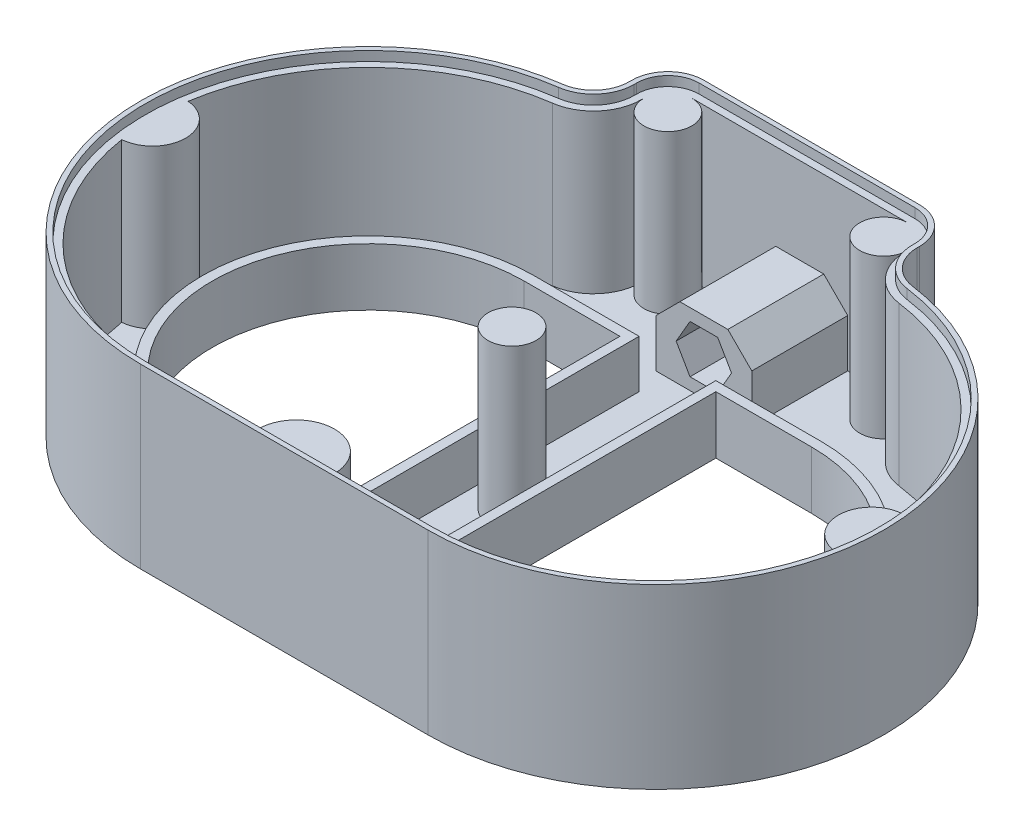
SolidWorks part; units mm, degrees
ref_plane "Front Plane" through (0, 0, 0) normal (0, 0, 1) x (1, 0, 0)
ref_plane "Top Plane" through (0, 0, 0) normal (0, 1, 0) x (1, 0, 0)
ref_plane "Right Plane" through (0, 0, 0) normal (1, 0, 0) x (0, 0, -1)
sketch "Sketch1" plane through (0, 0, 0) normal (0, 1, 0) x (1, 0, 0)
  line L0 (-30, 0) -> (30, 0) construction
  line L1 (-30, 32.5) -> (-10, 32.5)
  line L2 (-30, -32.5) -> (-10, -32.5)
  line L3 (-30, 54.4862) -> (-30, 55)
  line L4 (-30, -47.5) -> (30, -47.5)
  line L5 (-30, 47.5) -> (30, 47.5) construction
  line L6 (-22.5, 62.5) -> (22.5, 62.5)
  line L7 (30, 55) -> (30, 54.4862)
  line L8 (10, 32.5) -> (30, 32.5)
  line L10 (10, 32.5) -> (10, -32.5)
  line L12 (-10, 32.5) -> (-10, -32.5)
  line L13 (10, -32.5) -> (30, -32.5)
  line L14 (-30, 32.5) -> (30, 32.5) construction
  line L16 (-30, -32.5) -> (30, -32.5) construction
  arc A0 (-30, 32.5) -> (-30, -32.5) centre (-30, 0) ccw
  arc A1 (30, -32.5) -> (30, 32.5) centre (30, 0) ccw
  arc A2 (30, -47.5) -> (36.4773, 47.0563) centre (30, 0) ccw
  arc A3 (-36.4773, 47.0563) -> (-30, -47.5) centre (-30, 0) ccw
  arc A4 (22.5, 62.5) -> (30, 55) centre (22.5, 55) cw
  arc A5 (30, -47.5) -> (30, 47.5) centre (30, 0) ccw construction
  arc A6 (30, 54.4862) -> (36.4773, 47.0563) centre (37.5, 54.4862) ccw
  arc A7 (-30, 55) -> (-22.5, 62.5) centre (-22.5, 55) cw
  arc A8 (-30, 47.5) -> (-30, -47.5) centre (-30, 0) ccw construction
  arc A9 (-30, 54.4862) -> (-36.4773, 47.0563) centre (-37.5, 54.4862) cw
  point P2 (0, 0)
  point P23 (-30, 62.5)
  dimension "D2" = 32.5
  dimension "D5" = 7.5
  dimension "D1" = 60
  dimension "D4" = 20
  dimension "D6" = 20
  dimension "D3" = 15
extrude "Boss-Extrude1" add sketch "Sketch1" along normal blind 2
sketch "Sketch2" plane through (0, 2, 0) normal (0, 1, 0) x (1, 0, 0)
  line L4 (30, 54.4862) -> (30, 55)
  line L5 (22.5, 62.5) -> (-22.5, 62.5)
  line L6 (-30, 55) -> (-30, 54.4862)
  line L7 (-30, -47.5) -> (30, -47.5)
  line L8 (30, 54.4862) -> (30, 55)
  line L9 (22.5, 62.5) -> (-22.5, 62.5)
  line L10 (-30, 55) -> (-30, 54.4862)
  line L11 (-30, -47.5) -> (30, -47.5)
  arc A6 (30, -47.5) -> (36.4773, 47.0563) centre (30, 0) ccw
  arc A7 (30, 54.4862) -> (36.4773, 47.0563) centre (37.5, 54.4862) ccw
  arc A8 (30, 55) -> (22.5, 62.5) centre (22.5, 55) ccw
  arc A9 (-22.5, 62.5) -> (-30, 55) centre (-22.5, 55) ccw
  arc A10 (-36.4773, 47.0563) -> (-30, 54.4862) centre (-37.5, 54.4862) ccw
  arc A11 (-36.4773, 47.0563) -> (-30, -47.5) centre (-30, 0) ccw
  arc A12 (30, -47.5) -> (36.4773, 47.0563) centre (30, 0) ccw
  arc A13 (30, 54.4862) -> (36.4773, 47.0563) centre (37.5, 54.4862) ccw
  arc A14 (30, 55) -> (22.5, 62.5) centre (22.5, 55) ccw
  arc A15 (-22.5, 62.5) -> (-30, 55) centre (-22.5, 55) ccw
  arc A16 (-36.4773, 47.0563) -> (-30, 54.4862) centre (-37.5, 54.4862) ccw
  arc A17 (-36.4773, 47.0563) -> (-30, -47.5) centre (-30, 0) ccw
  dimension "D1" = 0
extrude "Extrude-Thin1" add sketch "Sketch2" along normal blind 35 thin thin type one direction reverse wall 1
sketch "Sketch5" plane through (0, 2, 0) normal (0, 1, 0) x (1, 0, 0)
  line L0 (10, -32.5) -> (10, 32.5)
  line L1 (10, 32.5) -> (30, 32.5)
  line L2 (30, -32.5) -> (10, -32.5)
  arc A0 (30, 32.5) -> (30, -32.5) centre (30, 0) cw
extrude "Extrude-Thin3" add sketch "Sketch5" along normal blind 10 thin thin type one direction wall 2
mirror "Mirror1" about plane through (0, 0, 0) normal (1, 0, 0) of "Extrude-Thin3"
sketch "Sketch6" plane through (0, 2, 0) normal (0, 1, 0) x (1, 0, 0)
  line L4 (29, 54.4862) -> (29, 55)
  line L5 (22.5, 61.5) -> (-22.5, 61.5)
  line L6 (-29, 55) -> (-29, 54.4862)
  line L7 (-30, -46.5) -> (30, -46.5)
  line L8 (29, 54.4862) -> (29, 55)
  line L9 (22.5, 61.5) -> (-22.5, 61.5)
  line L10 (-29, 55) -> (-29, 54.4862)
  line L11 (-30, -46.5) -> (30, -46.5)
  arc A6 (30, -46.5) -> (36.3409, 46.0656) centre (30, 0) ccw
  arc A7 (29, 54.4862) -> (36.3409, 46.0656) centre (37.5, 54.4862) ccw
  arc A8 (29, 55) -> (22.5, 61.5) centre (22.5, 55) ccw
  arc A9 (-22.5, 61.5) -> (-29, 55) centre (-22.5, 55) ccw
  arc A10 (-36.3409, 46.0656) -> (-29, 54.4862) centre (-37.5, 54.4862) ccw
  arc A11 (-36.3409, 46.0656) -> (-30, -46.5) centre (-30, 0) ccw
  arc A12 (30, -46.5) -> (36.3409, 46.0656) centre (30, 0) ccw
  arc A13 (29, 54.4862) -> (36.3409, 46.0656) centre (37.5, 54.4862) ccw
  arc A14 (29, 55) -> (22.5, 61.5) centre (22.5, 55) ccw
  arc A15 (-22.5, 61.5) -> (-29, 55) centre (-22.5, 55) ccw
  arc A16 (-36.3409, 46.0656) -> (-29, 54.4862) centre (-37.5, 54.4862) ccw
  arc A17 (-36.3409, 46.0656) -> (-30, -46.5) centre (-30, 0) ccw
  dimension "D1" = 0
extrude "Extrude-Thin4" add sketch "Sketch6" along normal blind 33 thin thin type one direction reverse wall 1.5
sketch "Sketch8" plane through (0, 2, 0) normal (0, 1, 0) x (1, 0, 0)
  line L0 (0, 0) -> (-75, 0) construction
  arc A0 (-36.1364, 44.5796) -> (-30, -45) centre (-30, 0) ccw construction
  arc A1 (-74.465, 6.9186) -> (-74.465, -6.9186) centre (-75, 0) cw
  arc A2 (-74.465, 6.9186) -> (-74.465, -6.9186) centre (-30, 0) ccw
  arc M9 (-36.1364, 44.5796) -> (-30, -45) centre (-30, 0) ccw
extrude "Boss-Extrude4" add sketch "Sketch8" along normal blind 33 contours L0 A1 M9 | A1 L0 A2
mirror "Mirror2" about plane through (0, 0, 0) normal (1, 0, 0) of "Boss-Extrude4"
sketch "Sketch9" plane through (0, 2, 0) normal (0, 1, 0) x (1, 0, 0)
  line L0 (-30, -45) -> (30, -45) construction
  line L1 (8, -45) -> (-8, -45)
  arc A0 (-8, -45) -> (8, -45) centre (0, -45) cw
  dimension "D1" = 8
extrude "Boss-Extrude5" add sketch "Sketch9" along normal blind 33
sketch "Sketch12" plane through (0, 2, 0) normal (0, 1, 0) x (1, 0, 0)
  circle A0 centre (-22.5, 55) radius 5
  circle A1 centre (22.5, 55) radius 5
extrude "Boss-Extrude7" add sketch "Sketch12" along normal blind 33
sketch "Sketch13" plane through (0, 2, 0) normal (0, 1, 0) x (1, 0, 0)
  line L0 (22.5, 60) -> (-22.5, 60) construction
  line L1 (10, 60) -> (-10, 60)
  line L2 (10, 60) -> (10, 40)
  line L3 (10, 40) -> (-10, 40)
  line L4 (-10, 60) -> (-10, 40)
  point P6 (0, 60)
  point P7 (0, 60)
  dimension "D1" = 20
  dimension "D2" = 20
extrude "Boss-Extrude8" add sketch "Sketch13" along normal blind 15
sketch "Sketch14" plane through (0, 0, -40) normal (0, 0, 1) x (1, 0, 0)
  line L0 (-10, 17) -> (10, 2) construction
  line L2 (5.7735, 9.5) -> (2.8868, 14.5)
  line L3 (2.8868, 14.5) -> (-2.8868, 14.5)
  line L4 (-2.8868, 14.5) -> (-5.7735, 9.5)
  line L5 (-5.7735, 9.5) -> (-2.8868, 4.5)
  line L6 (-2.8868, 4.5) -> (2.8868, 4.5)
  line L7 (2.8868, 4.5) -> (5.7735, 9.5)
  circle A0 centre (0, 9.5) radius 5 construction
  dimension "D1" = 10
extrude "Cut-Extrude1" cut sketch "Sketch14" against normal blind 28
chamfer "Chamfer2" distance 5 angle 45 2 edges at (-10, 17, -50) (10, 17, -50)
sketch "Sketch17" plane through (0, 2, 0) normal (0, 1, 0) x (1, 0, 0)
  line L0 (8, 0) -> (-8, 0) construction
  line L1 (8, 34.5) -> (8, -34.5) construction
  line L2 (-8, 34.5) -> (-8, -34.5) construction
  circle A0 centre (0, 0) radius 5
  dimension "D1" = 10
extrude "Boss-Extrude9" add sketch "Sketch17" along normal up to surface (33 mm away) up to face at (0, 35, -33.5124)
